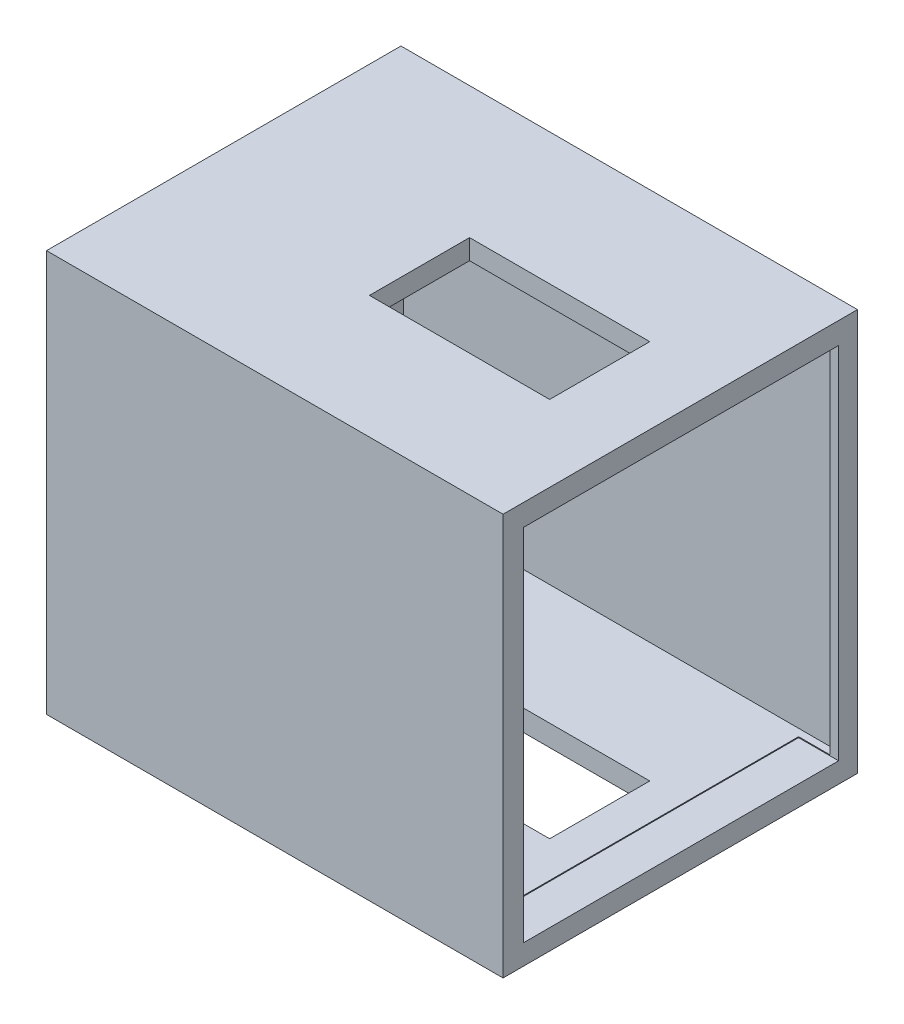
SolidWorks part; units mm, degrees
ref_plane "Front Plane" through (0, 0, 0) normal (0, 0, 1) x (1, 0, 0)
ref_plane "Top Plane" through (0, 0, 0) normal (0, 1, 0) x (1, 0, 0)
ref_plane "Right Plane" through (0, 0, 0) normal (1, 0, 0) x (0, 0, -1)
sketch "Sketch1" plane through (0, 0, 0) normal (0, 1, 0) x (1, 0, 0)
  line L1 (-114, 88.5) -> (114, 88.5)
  line L2 (-114, 88.5) -> (-114, -88.5)
  line L3 (-114, -88.5) -> (114, -88.5)
  line L4 (114, 88.5) -> (114, -88.5)
  line L5 (-114, 88.5) -> (114, -88.5) construction
  line L6 (-114, -88.5) -> (114, 88.5) construction
  line L7 (-14, 22.7687) -> (76, 22.7687)
  line L8 (-14, 22.7687) -> (-14, -27.2313)
  line L9 (-14, -27.2313) -> (76, -27.2313)
  line L10 (76, 22.7687) -> (76, -27.2313)
  line L11 (-14, 22.7687) -> (76, -27.2313) construction
  line L12 (-14, -27.2313) -> (76, 22.7687) construction
  point P0 (0, 0)
  point P6 (31, -2.2313)
  dimension "D1" = 228
  dimension "D2" = 177
  dimension "D3" = 90
  dimension "D4" = 50
  dimension "D5" = 100
  dimension "D6" = 38
extrude "Boss-Extrude2" add sketch "Sketch1" along normal blind 200.5826
sketch "Sketch2" plane through (0, 200.5826, 0) normal (0, 1, 0) x (1, 0, 0)
  line L1 (-106.9402, 82.7084) -> (1.8982, 82.7084)
  line L2 (-106.9402, 82.7084) -> (-106.9402, -82.0025)
  line L3 (-106.9402, -82.0025) -> (1.8982, -82.0025)
  line L4 (1.8982, 82.7084) -> (1.8982, -82.0025)
  line L5 (1.8982, 82.7084) -> (109.7929, 82.7084)
  line L6 (1.8982, 82.7084) -> (1.8982, 8.0294)
  line L7 (1.8982, 8.0294) -> (109.7929, 8.0294)
  line L8 (109.7929, 82.7084) -> (109.7929, 8.0294)
  line L9 (62.1808, 8.0294) -> (109.7929, 8.0294)
  line L10 (62.1808, 8.0294) -> (62.1808, -82.0025)
  line L11 (62.1808, -82.0025) -> (109.7929, -82.0025)
  line L12 (109.7929, 8.0294) -> (109.7929, -82.0025)
  line L13 (1.8982, -20.4626) -> (62.1808, -20.4626)
  line L14 (1.8982, -20.4626) -> (1.8982, -82.0025)
  line L15 (1.8982, -82.0025) -> (62.1808, -82.0025)
  line L16 (62.1808, -20.4626) -> (62.1808, -82.0025)
ref_plane "Plane1" through (0, 190.5826, 0) normal (0, 1, 0) x (1, 0, 0)
ref_plane "Plane2" through (0, 10, 0) normal (0, -1, 0) x (-1, 0, 0)
extrude "Cut-Extrude1" cut sketch "Sketch2" against normal blind 180 from surface at -10 contours L4 L1 L2 L3 | L8 L5 L4 L7 | L4 L15 L10 L13 | L12 L7 L10 L11 starting at plane "Plane1"
sketch "Sketch5" plane through (114, 0, 0) normal (1, 0, 0) x (0, 0, -1)
  line L2 (-78.226, 189.7889) -> (79.0774, 189.7889)
  line L3 (-78.226, 189.7889) -> (-78.226, 10.1429)
  line L4 (-78.226, 10.1429) -> (79.0774, 10.1429)
  line L5 (79.0774, 189.7889) -> (79.0774, 10.1429)
extrude "Cut-Extrude2" cut sketch "Sketch5" against normal blind 20 contours L3 L2 L5 L4
